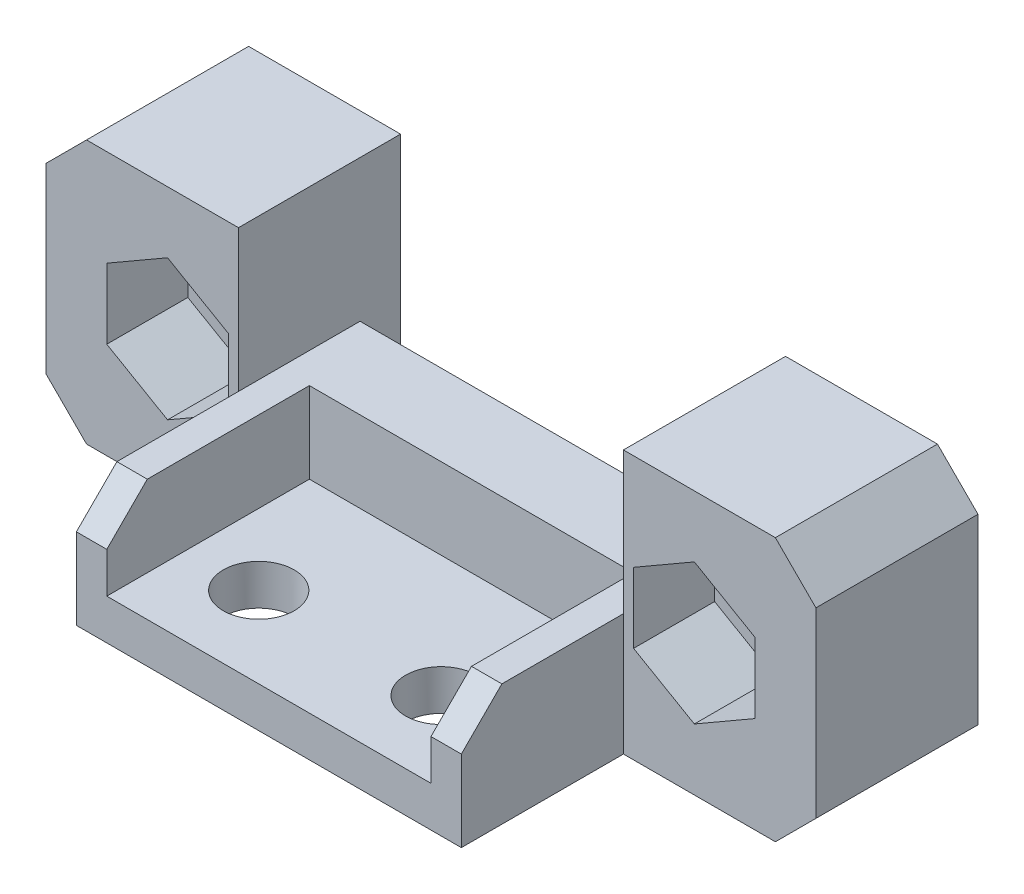
SolidWorks part; units mm, degrees
ref_plane "Front Plane" through (0, 0, 0) normal (0, 0, 1) x (1, 0, 0)
ref_plane "Top Plane" through (0, 0, 0) normal (0, 1, 0) x (1, 0, 0)
ref_plane "Right Plane" through (0, 0, 0) normal (1, 0, 0) x (0, 0, -1)
sketch "Sketch1" plane through (0, 0, 0) normal (0, 0, 1) x (1, 0, 0)
  line L1 (-19, 6.5) -> (19, 6.5)
  line L2 (-19, 6.5) -> (-19, -6.5)
  line L3 (-19, -6.5) -> (19, -6.5)
  line L4 (19, 6.5) -> (19, -6.5)
  line L5 (-19, 6.5) -> (19, -6.5) construction
  line L6 (-19, -6.5) -> (19, 6.5) construction
  point P0 (0, 0)
  dimension "D1" = 13
  dimension "D2" = 38
extrude "Boss-Extrude1" add sketch "Sketch1" along normal blind 8
sketch "Sketch2" plane through (0, 0, 8) normal (0, 0, 1) x (1, 0, 0)
  line L0 (19, 6.5) -> (-19, 6.5) construction
  line L1 (-9.5, -0.5) -> (9.5, -0.5)
  line L2 (-9.5, -0.5) -> (-9.5, 13.5)
  line L3 (-9.5, 13.5) -> (9.5, 13.5)
  line L4 (9.5, -0.5) -> (9.5, 13.5)
  line L5 (-9.5, -0.5) -> (9.5, 13.5) construction
  line L6 (-9.5, 13.5) -> (9.5, -0.5) construction
  line L7 (0, 6.5) -> (0, -0.1563) construction
  point P0 (0, 6.5)
  dimension "D1" = 19
  dimension "D2" = 7
extrude "Cut-Extrude1" cut sketch "Sketch2" against normal through all
sketch "Sketch3" plane through (0, 0, 8) normal (0, 0, 1) x (1, 0, 0)
  line L0 (-13, 0) -> (13, 0) construction
  circle A0 centre (-13, 0) radius 2
  circle A1 centre (13, 0) radius 2
  dimension "D2" = 4
  dimension "D1" = 26
extrude "Cut-Extrude2" cut sketch "Sketch3" against normal through all
sketch "Sketch4" plane through (0, 0, 8) normal (0, 0, 1) x (1, 0, 0)
  line L0 (-19, -6.5) -> (19, -6.5) construction
  line L1 (-9.5, -0.5) -> (9.5, -0.5)
  line L2 (-9.5, -0.5) -> (-9.5, -6.5)
  line L3 (-9.5, -6.5) -> (9.5, -6.5)
  line L4 (9.5, -0.5) -> (9.5, -6.5)
extrude "Boss-Extrude2" add sketch "Sketch4" along normal blind 8
sketch "Sketch5" plane through (0, -0.5, 0) normal (0, 1, 0) x (1, 0, 0)
  line L0 (-9.5, -12) -> (9.5, -12) construction
  line L1 (-9.5, -16) -> (-9.5, -8) construction
  line L2 (9.5, -16) -> (9.5, -8) construction
  circle A0 centre (-4.5, -12) radius 1.75
  circle A1 centre (4.5, -12) radius 1.75
  dimension "D3" = 3.5
  dimension "D1" = 5
  dimension "D2" = 5
extrude "Cut-Extrude3" cut sketch "Sketch5" against normal through all
sketch "Sketch6" plane through (0, 0, 8) normal (0, 0, 1) x (1, 0, 0)
  line L1 (-13, 3.4641) -> (-16, 1.7321)
  line L2 (-16, 1.7321) -> (-16, -1.7321)
  line L3 (-16, -1.7321) -> (-13, -3.4641)
  line L4 (-13, -3.4641) -> (-10, -1.7321)
  line L5 (-10, -1.7321) -> (-10, 1.7321)
  line L6 (-10, 1.7321) -> (-13, 3.4641)
  line L7 (13, -3.4641) -> (16, -1.7321)
  line L8 (16, -1.7321) -> (16, 1.7321)
  line L9 (16, 1.7321) -> (13, 3.4641)
  line L10 (13, 3.4641) -> (10, 1.7321)
  line L11 (10, 1.7321) -> (10, -1.7321)
  line L12 (10, -1.7321) -> (13, -3.4641)
  circle A0 centre (-13, 0) radius 3 construction
  circle A1 centre (13, 0) radius 3 construction
  dimension "D1" = 6
extrude "Cut-Extrude4" cut sketch "Sketch6" against normal blind 4
sketch "Sketch7" plane through (0, -0.5, 0) normal (0, 1, 0) x (1, 0, 0)
  line L0 (9.5, -16) -> (-9.5, -16) construction
  line L1 (-8, -16) -> (8, -16)
  line L2 (-8, -16) -> (-8, -6)
  line L3 (-8, -6) -> (8, -6)
  line L4 (8, -16) -> (8, -6)
  line L5 (-9.5, -16) -> (-9.5, -8) construction
  line L6 (9.5, -16) -> (9.5, -8) construction
  dimension "D1" = 10
  dimension "D2" = 1.5
  dimension "D3" = 1.5
extrude "Cut-Extrude5" cut sketch "Sketch7" against normal blind 4
chamfer "Chamfer1" distance 2 angle 45 6 edges at (19, -6.5, 4) (-19, -6.5, 4) (19, 6.5, 4) (-19, 6.5, 4) (8.75, -0.5, 16) (-8.75, -0.5, 16)
sketch "Sketch8" plane through (0, -0.5, 0) normal (0, 1, 0) x (1, 0, 0)
  line L0 (9.5, 0) -> (9.5, -8) construction
  line L1 (-9.5, 0) -> (9.5, 0)
  line L2 (-9.5, 0) -> (-9.5, -2)
  line L3 (-9.5, -2) -> (9.5, -2)
  line L4 (9.5, 0) -> (9.5, -2)
  point P5 (9.5, -2.7712)
  dimension "D1" = 2
extrude "Cut-Extrude6" cut sketch "Sketch8" against normal through all
